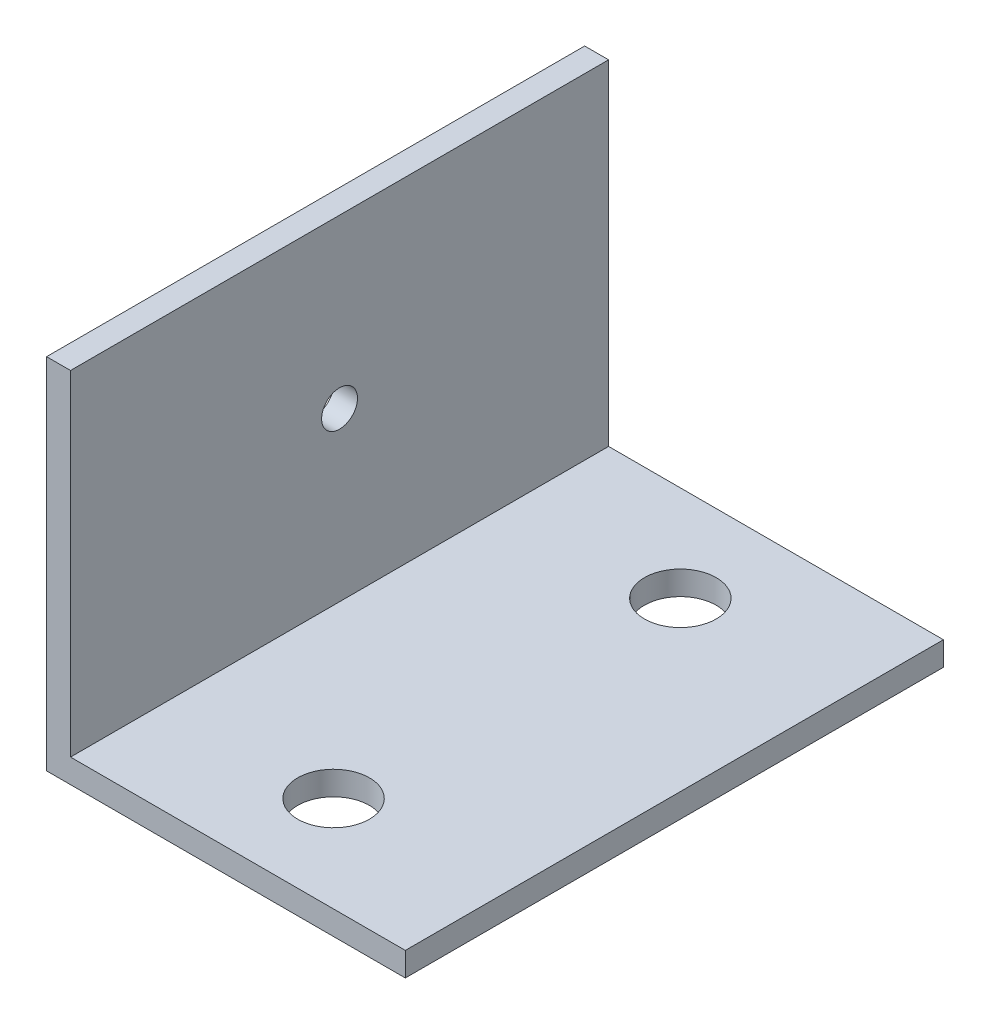
SolidWorks part; units mm, degrees
ref_plane "Přední rovina" through (0, 0, 0) normal (0, 0, 1) x (1, 0, 0)
ref_plane "Horní rovina" through (0, 0, 0) normal (0, 1, 0) x (1, 0, 0)
ref_plane "Pravá rovina" through (0, 0, 0) normal (1, 0, 0) x (0, 0, -1)
sketch "Skica1" plane through (0, 0, 0) normal (0, 0, 1) x (1, 0, 0)
  line L0 (-63.4709, 45.7822) -> (-63.4709, 15.7822)
  line L1 (-63.4709, 15.7822) -> (-33.4709, 15.7822)
  line L2 (-33.4709, 15.7822) -> (-33.4709, 17.7822)
  line L3 (-33.4709, 17.7822) -> (-61.4709, 17.7822)
  line L4 (-61.4709, 17.7822) -> (-61.4709, 45.7822)
  line L5 (-61.4709, 45.7822) -> (-63.4709, 45.7822)
  dimension "D1" = 30
  dimension "D2" = 2
extrude "Přidat vysunutím1" add sketch "Skica1" along normal blind 45
sketch "Skica2" plane through (0, 17.7822, 0) normal (0, 1, 0) x (1, 0, 0)
  line L0 (-61.4709, -45) -> (-33.4709, -45)
  line L1 (-47.4709, -45) -> (-47.4709, 0)
  line L2 (-33.4709, 0) -> (-61.4709, 0) construction
  point P8 (-47.4709, -8)
  point P9 (-47.4709, -37)
  dimension "D1" = 8
  dimension "D2" = 8
hole_wizard "Díry pro kolík, velikost mm1" positions "Skica3" profile "Skica4" hole size "Ø6.0" standard "ANSI Metric" end condition through all
sketch "Skica3" plane through (0, 17.7822, 0) normal (0, 1, 0) x (1, 0, 0)
  point P0 (-47.4709, -37)
  point P3 (-47.4709, -8)
sketch "Skica4" plane through (-47.4709, 17.7822, 37) normal (1, 0, 0) x (0, 0, 1)
  line L0 (0, 0) -> (0, 2)
  line L1 (0, 2) -> (3, 2)
  line L2 (3, 2) -> (3, 0)
  line L5 (3, 0) -> (0, 0)
  line L11 (0, -6.35) -> (0, 107.95) construction
  dimension "Průměr díry skrz" = 6
  dimension "Hloubka díry skrz" = 2
sketch "Skica5" plane through (-61.4709, 0, 0) normal (1, 0, 0) x (0, 0, -1)
  line L0 (-45, 17.7822) -> (-45, 45.7822)
  line L1 (-45, 31.7822) -> (0, 31.7822)
  line L2 (0, 17.7822) -> (0, 45.7822) construction
  point P8 (-22.5, 31.7822)
hole_wizard "Díry pro kolík, velikost mm2" positions "Skica6" profile "Skica7" hole size "Ø3.0" standard "ANSI Metric" end condition through all
sketch "Skica6" plane through (-61.4709, 0, 0) normal (1, 0, 0) x (0, 0, -1)
  point P0 (-22.5, 31.7822)
sketch "Skica7" plane through (-61.4709, 31.7822, 22.5) normal (0, 1, 0) x (0, 0, -1)
  line L0 (0, 0) -> (0, 2)
  line L1 (0, 2) -> (1.5, 2)
  line L2 (1.5, 2) -> (1.5, 0)
  line L5 (1.5, 0) -> (0, 0)
  line L11 (0, -6.35) -> (0, 107.95) construction
  dimension "Průměr díry skrz" = 3
  dimension "Hloubka díry skrz" = 2
